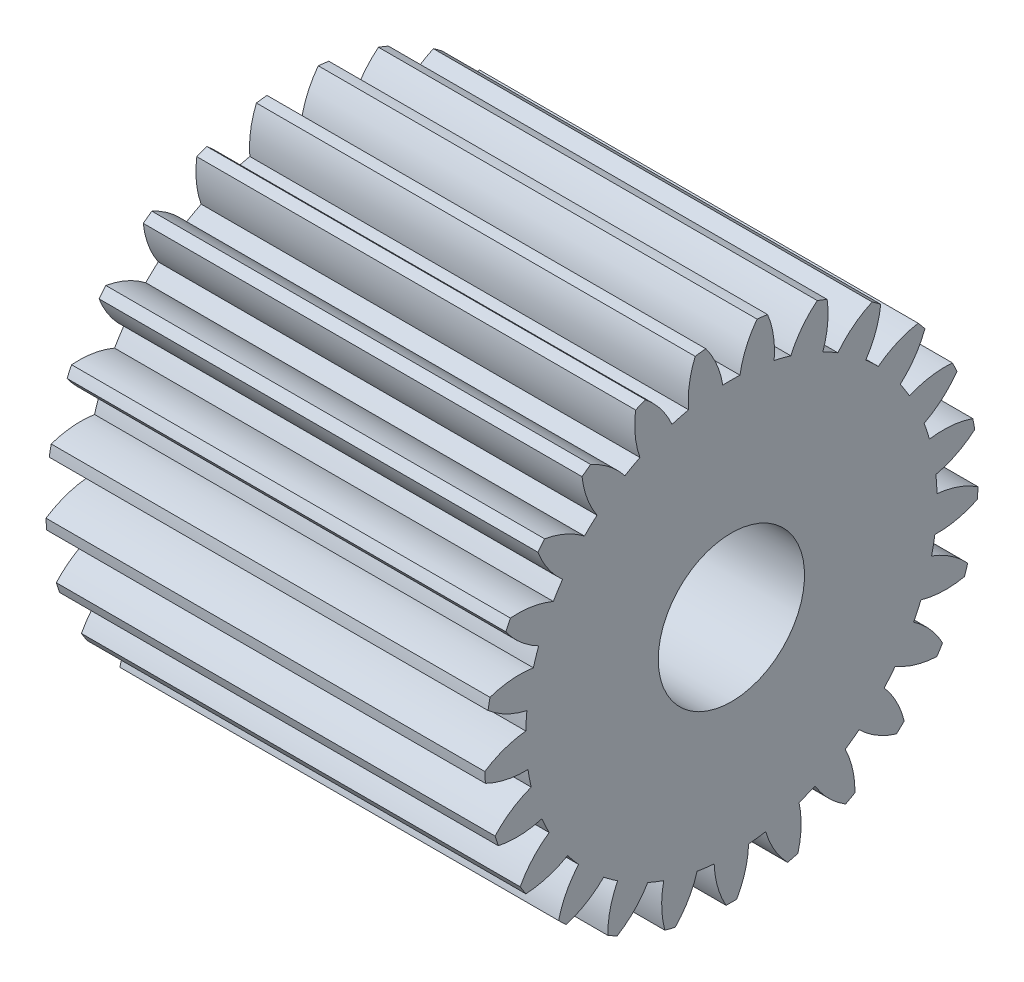
SolidWorks part; units mm, degrees
material "ABS"
ref_plane "Plane1" through (0, 0, 0) normal (0, 0, 1) x (1, 0, 0)
ref_plane "Plane2" through (0, 0, 0) normal (0, 1, 0) x (1, 0, 0)
ref_plane "Plane3" through (0, 0, 0) normal (1, 0, 0) x (0, 0, -1)
sketch "HoldingSke" plane through (0, 0, 0) normal (0, 1, 0) x (1, 0, 0)
  line L0 (0, 0) -> (3.6252, -1.6905)
  line L1 (-15, 0) -> (100, 0) construction
  line L2 (0, 0) -> (-2.1039, 2.3779)
  line L3 (0, 0) -> (-11.863, 4.5341)
  line L4 (0, 0) -> (7.8269, 3.6497)
  line L5 (0, 0) -> (-46.8476, -17.4728)
  line L6 (0, 0) -> (-4.9738, -3.3558)
  line L7 (-2.1039, 2.3779) -> (8.6586, 51.2059)
  line L8 (-76.2, 54.61) -> (-75.9, 54.61)
  line L9 (-71.009, 38.7566) -> (-53.1078, 45.2721)
  line L10 (-76.2, 71.12) -> (104.1128, 71.12)
  line L11 (0, 0) -> (-6, 0)
  line L12 (-76.2, 101.6) -> (-76.192, 101.6)
  line L13 (24.9733, 27.94) -> (52.9518, 28.4284)
  line L14 (24.9733, 27.94) -> (24.9743, 27.94)
  line L15 (24.9733, 27.94) -> (100.4006, 29.5858)
  line L16 (-63.627, -0.25) -> (-12.827, -0.25)
  circle A0 centre (0, 0) radius 1
  circle A1 centre (0, 0) radius 2.8115
  circle A2 centre (0, 0) radius 37.5
  circle A3 centre (0, 0) radius 1
  dimension "MHD" = 5.623
  dimension "Hub_dia" = 75
  dimension "Bore" = 2
  dimension "MBD" = 2
  dimension "Num_teeth" = 25
  dimension "Pitch" = 4
  dimension "Overall_len" = 50
  dimension "Show_teeth" = 25
  dimension "Thickness" = 6
  dimension "OAL" = 50.0001
  dimension "T_dim" = 0.3
  dimension "Ap" = 20
  dimension "H" = 19.05
  dimension "Pitch_radius" = 180.3128
  dimension "Width" = 6
  dimension "Backlash" = 0.008
  dimension "Addendum_fac" = 1
  dimension "Dedendum_fac" = 1.25
  dimension "Clearance_fac" = 0.25
  dimension "Dedendum_add" = 0.001
  dimension "Module" = 0.25
sketch "BasProSke" plane through (0, 0, 0) normal (0, 1, 0) x (1, 0, 0)
  line L0 (-10, 0) -> (60, 0) construction
  line L1 (0, 0) -> (0, 3.375)
  line L2 (0, 0) -> (6, 0)
  line L3 (6, 0) -> (6, 3.375)
  line L4 (6, 3.375) -> (0, 3.375)
  dimension "Thickness" = 6
  dimension "Diameter" = 6.75
revolve "Base-Revolve" add sketch "BasProSke" angle 360 about L0
sketch "TooCutSke" plane through (0, 0, 0) normal (1, 0, 0) x (0, 0, -1)
  line L1 (0, 0) -> (0, 107) construction
  line L2 (0, 0) -> (-0.2102, 3.1179) construction
  line L3 (0, 0) -> (-0.782, 6.1902) construction
  line L4 (-0.2102, 3.1179) -> (-0.391, 3.0951) construction
  arc A0 (0.1175, 2.809) -> (-0.1175, 2.809) centre (0, 0) ccw
  arc A1 (0.3689, 3.3803) -> (-0.3689, 3.3803) centre (0, 0) ccw
  circle A2 centre (0, 0) radius 3.125 construction
  circle A3 centre (0, 0) radius 2.9365 construction
  arc A4 (-0.1175, 2.809) -> (-0.3689, 3.3803) centre (-1.3511, 2.6072) ccw
  arc A5 (0.3689, 3.3803) -> (0.1175, 2.809) centre (1.3511, 2.6072) ccw
  dimension "Root_dia" = 5.623
  dimension "Overcut_dia" = 6.8008
  dimension "Pitch_dia" = 6.25
  dimension "Base_dia" = 5.8731
  dimension "Flank_rad" = 1.25
  dimension "Half_ang" = 7.2
  dimension "Half_CT" = 0.1822
extrude "ToothCut" cut sketch "TooCutSke" along normal through all
fillet "Breaks" [suppressed] radius 0.005
fillet "RootFillets" [suppressed] radius 0.0635
pattern_circular "TeethCuts" count 25 every 14.4 about axis through (-10, 0, 0) along (1, 0, 0) of "ToothCut", "RootFillets", "Breaks"
sketch "HubNeaOneSke" plane through (0, 0, 0) normal (-1, 0, 0) x (0, 0, 1)
  circle A0 centre (0, 0) radius 2.8115
  dimension "Diameter" = 5.623
extrude "HubNearOne" [suppressed] add sketch "HubNeaOneSke" along normal blind 44.0001
sketch "HubNeaBotSke" plane through (0, 0, 0) normal (-1, 0, 0) x (0, 0, 1)
  circle A0 centre (0, 0) radius 2.8115
  dimension "Diameter" = 5.623
extrude "HubNearBoth" [suppressed] add sketch "HubNeaBotSke" along normal blind 22
ref_plane "FarPln" through (6, 0, 0) normal (1, 0, 0) x (0, 0, -1)
sketch "HubFarSke" plane through (6, 0, 0) normal (1, 0, 0) x (0, 0, -1)
  circle A0 centre (0, 0) radius 2.8115
  dimension "Diameter" = 5.623
extrude "HubFar" [suppressed] add sketch "HubFarSke" along normal blind 22
sketch "BorSke" plane through (0, 0, 0) normal (1, 0, 0) x (0, 0, -1)
  circle A0 centre (0, 0) radius 1
  dimension "Diameter" = 2
extrude "Bore" cut sketch "BorSke" along normal mid plane 100.0001
sketch "KeySke" plane through (0, 0, 0) normal (1, 0, 0) x (0, 0, -1)
  line L0 (-0.4, 0) -> (-0.4, 1.3)
  line L1 (-0.4, 1.3) -> (0.4, 1.3)
  line L2 (0.4, 1.3) -> (0.4, 0)
  line L3 (0, 0) -> (0, 34) construction
  line L4 (-0.4, 0) -> (0.4, 0)
  dimension "Offset" = 1.3
  dimension "Width" = 0.8
extrude "Keyway" [suppressed] cut sketch "KeySke" along normal mid plane 100.0001
pattern_circular "Keyway2" [suppressed] count 2 every 90 about axis through (-10, 0, 0) along (1, 0, 0)
equation "' \"Module@HoldingSke\" = 6.35"
equation "' \"Num_teeth@HoldingSke\" = 12"
equation "' \"Ap@HoldingSke\" =  20"
equation "' \"Ap@HoldingSke\" = 20"
equation "' \"Width@HoldingSke\" = 0.5 * 25.4"
equation "' \"Hub_dia@HoldingSke\"= 1 * 25.4"
equation "' \"Hub_dia@HoldingSke\" = 1 * 25.4"
equation "' \"Overall_len@HoldingSke\" = 1.0 * 25.4"
equation "' \"Bore@HoldingSke\" = 0.75 * 25.4"
equation "' \"T_dim@HoldingSke\" = 0.1 * 25.4"
equation "' \"Width@KeySke\" = 0.25 * 25.4"
equation "' \"Show_teeth@HoldingSke\" = 13"
equation "' \"Backlash@HoldingSke\" = 0.009 * 25.4"
equation "' \"Addendum_fac@HoldingSke\" = 1.0"
equation "' \"Dedendum_fac@HoldingSke\" = 1.25"
equation "' \"Dedendum_add@HoldingSke\" = 0.00005 * 25.4"
equation "' \"Clearance_fac@HoldingSke\" = 0.25"
equation "\"Pitch@HoldingSke\" = 1 / \"Module@HoldingSke\""
equation "\"Overcut_dia@TooCutSke\" = (\"Num_teeth@HoldingSke\" + 2 * \"Addendum_fac@HoldingSke\") / \"Pitch@HoldingSke\" + 0.002 * 25.4"
equation "\"Pitch_dia@TooCutSke\" = \"Num_teeth@HoldingSke\" / \"Pitch@HoldingSke\""
equation "\"Base_dia@TooCutSke\" = \"Num_teeth@HoldingSke\" / \"Pitch@HoldingSke\" * cos((\"Ap@HoldingSke\"  * 3.14159265 / 180))"
equation "\"Root_dia@TooCutSke\" = (\"Num_teeth@HoldingSke\" + 2) / \"Pitch@HoldingSke\" - 2 * (\"Addendum_fac@HoldingSke\" + \"Dedendum_fac@HoldingSke\") / \"Pitch@HoldingSke\" - \"Dedendum_add@HoldingSke\" * 2"
equation "\"Half_ang@TooCutSke\" = 180 / \"Num_teeth@HoldingSke\""
equation "\"Half_CT@TooCutSke\" = \"Num_teeth@HoldingSke\" / \"Pitch@HoldingSke\" * sin((3.14159265 / 2 / \"Num_teeth@HoldingSke\")) / 2 - 7 * \"Backlash@HoldingSke\" / 4"
equation "\"Flank_rad@TooCutSke\" = \"Num_teeth@HoldingSke\" / \"Pitch@HoldingSke\" / 5"
equation "\"Radius@RootFillets\" = \"Clearance_fac@HoldingSke\" / \"Pitch@HoldingSke\" + \"Dedendum_add@HoldingSke\""
equation "\"Break_rad@Breaks\" = 0.02 / \"Pitch@HoldingSke\""
equation "\"Thickness@HoldingSke\" = \"Width@HoldingSke\""
equation "\"OAL@HoldingSke\" = \"Thickness@HoldingSke\""
equation "\"MHD@HoldingSke\" = (\"Num_teeth@HoldingSke\" + 2) / \"Pitch@HoldingSke\" - 2 * (\"Addendum_fac@HoldingSke\" + \"Dedendum_fac@HoldingSke\")  / \"Pitch@HoldingSke\" - \"Dedendum_add@HoldingSke\" * 2"
equation "\"MBD@HoldingSke\" = (\"Num_teeth@HoldingSke\" + 2) / \"Pitch@HoldingSke\" - 2 * (\"Addendum_fac@HoldingSke\" + \"Dedendum_fac@HoldingSke\")  / \"Pitch@HoldingSke\" - \"Dedendum_add@HoldingSke\" * 2 - 0.002 * 25.4"
equation "\"MHD@HoldingSke\" = ((sgn( \"MHD@HoldingSke\" - \"Hub_dia@HoldingSke\" )-1)*( \"MHD@HoldingSke\" - \"Hub_dia@HoldingSke\" ))/-2+ \"Hub_dia@HoldingSke\""
equation "\"MBD@HoldingSke\" = ((sgn( \"MBD@HoldingSke\" - \"Bore@HoldingSke\" )-1)*( \"MBD@HoldingSke\" - \"Bore@HoldingSke\" ))/-2+ \"Bore@HoldingSke\""
equation "\"OAL@HoldingSke\" = ((sgn( \"OAL@HoldingSke\" - \"Overall_len@HoldingSke\" )+1)*( \"OAL@HoldingSke\" - \"Overall_len@HoldingSke\" ))/2 + \"Overall_len@HoldingSke\" + 0.000002 * 25.4"
equation "\"Num_teeth@TeethCuts\" = int( \"Show_teeth@HoldingSke\" ) + 1"
equation "\"Num_teeth@TeethCuts\" = ((sgn( \"Num_teeth@TeethCuts\" - \"Num_teeth@HoldingSke\" )-1)*( \"Num_teeth@TeethCuts\" - \"Num_teeth@HoldingSke\" ))/-2+ \"Num_teeth@HoldingSke\""
equation "\"Num_teeth@TeethCuts\" = ((sgn( \"Num_teeth@TeethCuts\" - 2.0)+1)*( \"Num_teeth@TeethCuts\" - 2.0))/2 +2.0"
equation "\"Angle@TeethCuts\" = 360.0 / \"Num_teeth@HoldingSke\""
equation "\"Diameter@BasProSke\" = (\"Num_teeth@HoldingSke\" + 2 * \"Addendum_fac@HoldingSke\") / \"Pitch@HoldingSke\""
equation "\"Thickness@BasProSke\"  = \"Thickness@HoldingSke\""
equation "' \"Fillet_rad@BasProSke\" =  \"Thickness@HoldingSke\" * 0.05"
equation "' \"Fillet_rad@BasProSke\" = \"Thickness@HoldingSke\" * 0.05"
equation "\"MHD@HoldingSke\" = ((sgn( \"MHD@HoldingSke\" - \"Root_dia@TooCutSke\" )-1)*( \"MHD@HoldingSke\" - \"Root_dia@TooCutSke\" ))/-2+ \"Root_dia@TooCutSke\""
equation "\"Diameter@HubNeaOneSke\" = \"MHD@HoldingSke\""
equation "\"Length@HubNearOne\" = \"OAL@HoldingSke\" - \"Thickness@BasProSke\""
equation "\"Diameter@HubNeaBotSke\" = \"MHD@HoldingSke\""
equation "\"Length@HubNearBoth\" = ( \"OAL@HoldingSke\" - \"Thickness@BasProSke\" ) / 2.0"
equation "\"Thickness@FarPln\" = \"Thickness@BasProSke\""
equation "\"Diameter@HubFarSke\" = \"MHD@HoldingSke\""
equation "\"Length@HubFar\" = ( \"OAL@HoldingSke\" - \"Thickness@BasProSke\" ) / 2.0"
equation "\"Diameter@BorSke\" = \"MBD@HoldingSke\""
equation "\"D1@Bore\" = \"OAL@HoldingSke\" * 2.0"
equation "\"D1@Keyway\" = \"OAL@HoldingSke\" * 2.0"
equation "\"Offset@KeySke\" = \"T_dim@HoldingSke\" + \"MBD@HoldingSke\" / 2.0"
